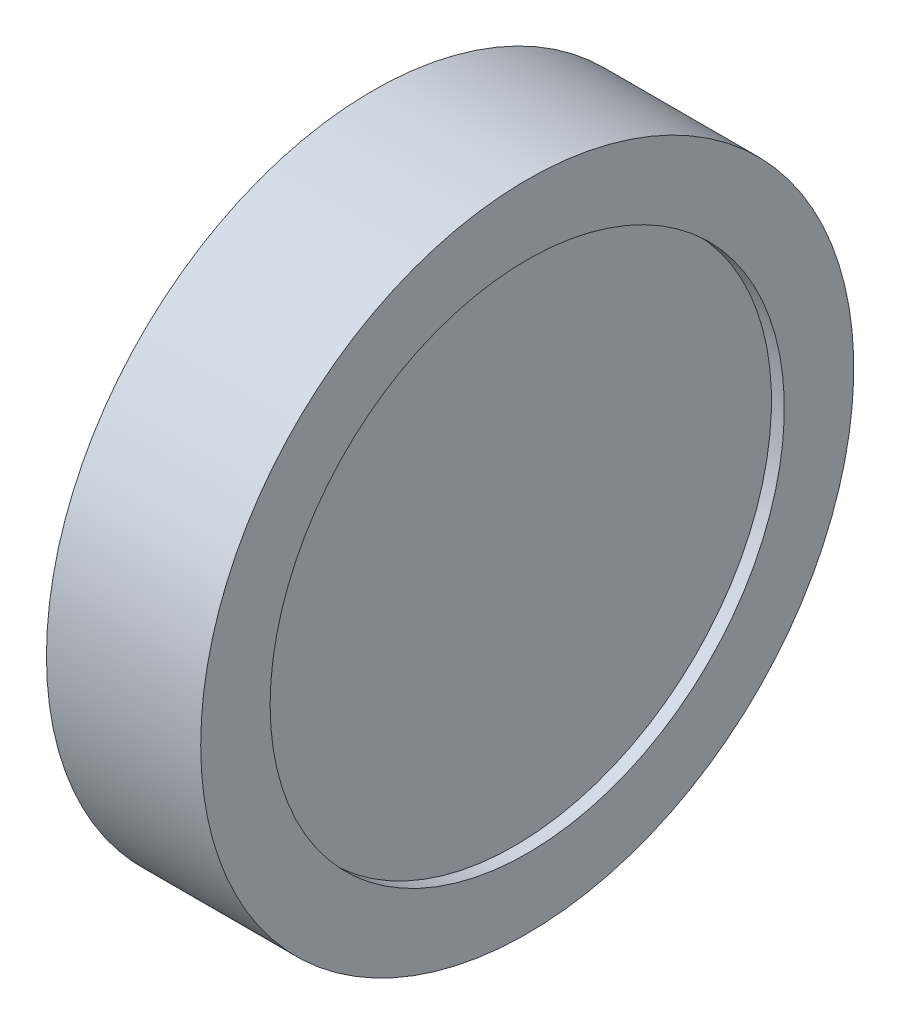
SolidWorks part; units mm, degrees
ref_plane "前视基准面" through (0, 0, 0) normal (0, 0, 1) x (1, 0, 0)
ref_plane "上视基准面" through (0, 0, 0) normal (0, 1, 0) x (1, 0, 0)
ref_plane "右视基准面" through (0, 0, 0) normal (1, 0, 0) x (0, 0, -1)
sketch "草图1" plane through (0, 0, 0) normal (0, 0, 1) x (1, 0, 0)
  line L0 (-2.5, 10) -> (-2.5, 0)
  line L2 (-2.5, 10) -> (2.5, 10)
  line L3 (-2.5, 0) -> (2.5, 0)
  line L4 (2.5, 10) -> (2.5, 0)
revolve "旋转2" add sketch "草图1" angle 360 about L3
sketch "草图4" plane through (0, 0, 0) normal (0, 0, 1) x (1, 0, 0)
  line L0 (-3, 12.7) -> (3, 12.7)
  line L1 (3, 12.7) -> (3, 10)
  line L2 (3, 10) -> (-3, 10)
  line L3 (2.5, 10) -> (-2.5, 10) construction
  line L4 (-3, 10) -> (-3, 12.7)
  line L5 (0, 10) -> (0, 12.7) construction
  line L6 (-1.6142, 0) -> (1.5903, 0) construction
revolve "旋转3" add sketch "草图4" angle 360 about L6
equation "\"D1@草图4\"=\"D1@草图1\""
